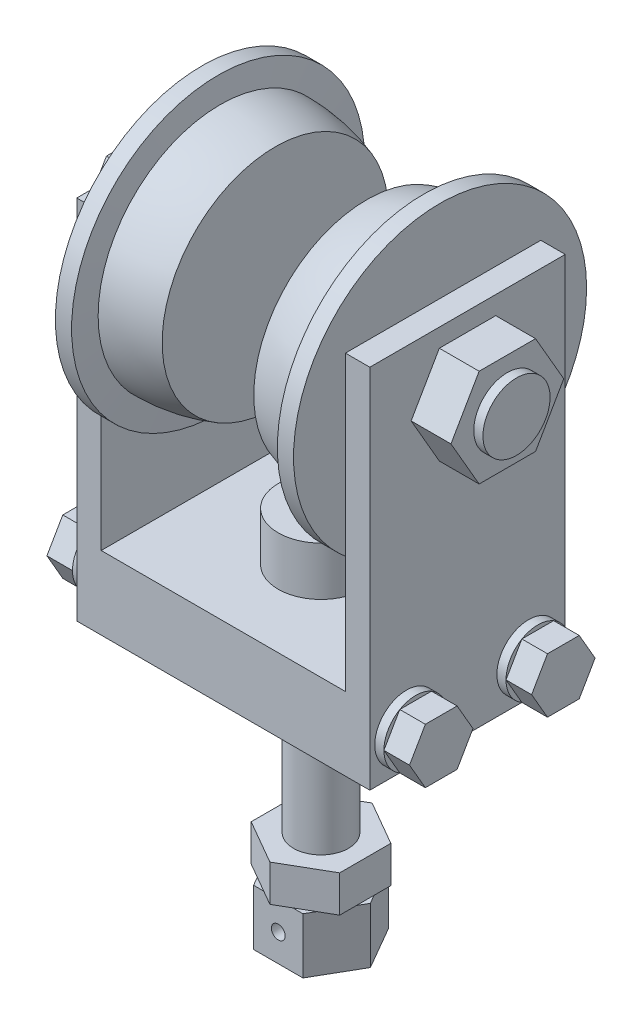
SolidWorks part; units mm, degrees
ref_plane "Front" through (0, 0, 0) normal (0, 0, 1) x (1, 0, 0)
ref_plane "Top" through (0, 0, 0) normal (0, 1, 0) x (1, 0, 0)
ref_plane "Right" through (0, 0, 0) normal (1, 0, 0) x (0, 0, -1)
ref_plane "Z PLANE" through (0, 0, 0) normal (0, 0, 1) x (1, 0, 0)
ref_plane "YOKE BOTTOM" through (0, 0, 0) normal (0, 1, 0) x (-1, 0, 0)
ref_plane "X PLANE" through (0, 0, 0) normal (1, 0, 0) x (0, 0, -1)
sketch "YOKE CROSS SECTION" plane through (0, 0, 0) normal (1, 0, 0) x (0, 0, -1)
  line L0 (0, 0) -> (0, 57.0916) construction
  line L1 (0, 84.8167) -> (0, -84.8167) construction
  line L2 (-50.8, 0) -> (50.8, 0)
  line L3 (69.1602, 0) -> (-69.1602, 0) construction
  line L4 (50.8, 0) -> (50.8, 38.1)
  line L5 (-50.8, 0) -> (-50.8, 38.1)
  line L6 (50.8, 38.1) -> (-50.8, 38.1)
  point P12 (0, 38.1)
  dimension "D1" = 38.1
  dimension "D2" = 101.6
ref_plane "1/2 YOKE LENGTH (A)" through (63.5, 0, 0) normal (1, 0, 0) x (0, 0, -1)
extrude "YOKE" add sketch "YOKE CROSS SECTION" along normal up to surface (63.5 mm away) up to plane "1/2 YOKE LENGTH (A)"
sketch "SIDEPLATE PROFILE" plane through (63.5, 0, 0) normal (1, 0, 0) x (0, 0, -1)
  line L0 (0, 0) -> (0, 74.7424) construction
  line L1 (0, 84.8167) -> (0, -84.8167) construction
  line L2 (-50.8, 0) -> (50.8, 0)
  line L3 (50.8, 0) -> (50.8, 190.5)
  line L4 (-50.8, 0) -> (-50.8, 190.5)
  line L5 (50.8, 190.5) -> (-50.8, 190.5)
  point P11 (0, 190.5)
  dimension "D1" = 190.5
ref_plane "WHEEL HEIGHT" through (0, 155.575, 0) normal (0, 1, 0) x (-1, 0, 0)
ref_plane "SCREW LOCATION X" through (0, 0, 31.75) normal (0, 0, 1) x (1, 0, 0)
ref_plane "SCREW LOCATION Y" through (0, 19.05, 0) normal (0, 1, 0) x (-1, 0, 0)
extrude "SIDEPLATE" add sketch "SIDEPLATE PROFILE" along normal blind 12.7
sketch "WHEEL PIN NUT PROFILE" plane through (76.2, 0, 0) normal (1, 0, 0) x (0, 0, -1)
  line L0 (0, 84.8167) -> (0, -84.8167) construction
  line L1 (29.3294, 155.575) -> (14.6647, 180.975)
  line L2 (14.6647, 180.975) -> (-14.6647, 180.975)
  line L3 (-14.6647, 180.975) -> (-29.3294, 155.575)
  line L4 (-29.3294, 155.575) -> (-14.6647, 130.175)
  line L5 (-14.6647, 130.175) -> (14.6647, 130.175)
  line L6 (14.6647, 130.175) -> (29.3294, 155.575)
  line L7 (69.1602, 155.575) -> (-69.1602, 155.575) construction
  circle A0 centre (0, 155.575) radius 25.4 construction
  dimension "D1" = 50.8
extrude "WHEEL PIN NUT" add sketch "WHEEL PIN NUT PROFILE" along normal blind 20.701
sketch "WHEEL PIN PROJECTION PROFILE" plane through (96.901, 0, 0) normal (1, 0, 0) x (0, 0, -1)
  line L0 (0, 84.8167) -> (0, -84.8167) construction
  line L1 (69.1602, 155.575) -> (-69.1602, 155.575) construction
  circle A0 centre (0, 155.575) radius 17.4625
  dimension "D1" = 34.925
extrude "WHEEL PIN PROJECTION" add sketch "WHEEL PIN PROJECTION PROFILE" along normal blind 4.7625
sketch "LOCKNUTS PROFILE" plane through (76.2, 0, 0) normal (1, 0, 0) x (0, 0, -1)
  line L0 (-31.75, 84.8167) -> (-31.75, -84.8167) construction
  line L1 (50, 19.05) -> (-50, 19.05) construction
  circle A0 centre (-31.75, 19.05) radius 16.4973
  dimension "D1" = 32.9946
extrude "LOCKNUTS" add sketch "LOCKNUTS PROFILE" along normal blind 4.7625
sketch "SCREWS PROFILE" plane through (80.9625, 0, 0) normal (1, 0, 0) x (0, 0, -1)
  line L0 (50, 19.05) -> (-50, 19.05) construction
  line L1 (-15.2522, 19.05) -> (-23.5011, 33.3375)
  line L2 (-23.5011, 33.3375) -> (-39.9989, 33.3375)
  line L3 (-39.9989, 33.3375) -> (-48.2478, 19.05)
  line L4 (-48.2478, 19.05) -> (-39.9989, 4.7625)
  line L5 (-39.9989, 4.7625) -> (-23.5011, 4.7625)
  line L6 (-23.5011, 4.7625) -> (-15.2522, 19.05)
  line L7 (-31.75, 84.8167) -> (-31.75, -84.8167) construction
  circle A0 centre (-31.75, 19.05) radius 14.2875 construction
  dimension "D1" = 28.575
extrude "SCREWS" add sketch "SCREWS PROFILE" along normal blind 13.3096
sketch "PROFILE" plane through (0, 38.1, 0) normal (0, 1, 0) x (-1, 0, 0)
  line L0 (84.8167, 0) -> (-84.8167, 0) construction
  line L1 (0, 83.2389) -> (0, -83.2389) construction
  circle A0 centre (0, 0) radius 22.225
  dimension "D1" = 44.45
extrude "KING BOLT HEAD" add sketch "PROFILE" along normal blind 25.4
mirror "Mirror1" about plane through (0, 0, 0) normal (0, 0, 1) of "SCREWS", "LOCKNUTS"
mirror "Mirror5" about plane through (0, 0, 0) normal (1, 0, 0) of bodies 112
ref_plane "TOP OF NUT" through (0, -82.55, 0) normal (0, 1, 0) x (-1, 0, 0)
sketch "DIA." plane through (0, 0, 0) normal (0, -1, 0) x (1, 0, 0)
  line L0 (84.8167, 0) -> (-84.8167, 0) construction
  line L1 (0, -83.2389) -> (0, 83.2389) construction
  circle A0 centre (0, 0) radius 14.2875
  dimension "D1" = 28.575
extrude "KING BOLT" add sketch "DIA." along normal up to surface (82.55 mm away) up to plane "TOP OF NUT"
sketch "KING BOLT JAN NUT PROFILE" plane through (0, -82.55, 0) normal (0, -1, 0) x (1, 0, 0)
  line L0 (84.8167, 0) -> (-84.8167, 0) construction
  line L1 (0, -26.5798) -> (23.0188, -13.2899)
  line L2 (23.0188, -13.2899) -> (23.0187, 13.2899)
  line L3 (23.0187, 13.2899) -> (0, 26.5798)
  line L4 (0, 26.5798) -> (-23.0188, 13.2899)
  line L5 (-23.0188, 13.2899) -> (-23.0188, -13.2899)
  line L6 (-23.0188, -13.2899) -> (0, -26.5798)
  line L7 (0, -83.2389) -> (0, 83.2389) construction
  circle A0 centre (0, 0) radius 23.0188 construction
  dimension "D1" = 46.0375
extrude "KING BOLT JAM NUT" add sketch "KING BOLT JAN NUT PROFILE" along normal blind 19.05
sketch "KING BOLT NUT PROFILE" plane through (0, -101.6, 0) normal (0, -1, 0) x (1, 0, 0)
  line L1 (25.6632, 0) -> (12.8316, 22.225)
  line L2 (12.8316, 22.225) -> (-12.8316, 22.225)
  line L3 (-12.8316, 22.225) -> (-25.6632, 0)
  line L4 (-25.6632, 0) -> (-12.8316, -22.225)
  line L5 (-12.8316, -22.225) -> (12.8316, -22.225)
  line L6 (12.8316, -22.225) -> (25.6632, 0)
  line L10 (0, -83.2389) -> (0, 83.2389) construction
  line L11 (84.8167, 0) -> (-84.8167, 0) construction
  circle A0 centre (0, 0) radius 22.225 construction
  dimension "D1" = 44.45
extrude "KING BOLT NUT" add sketch "KING BOLT NUT PROFILE" along normal blind 28.9306
sketch "Sketch5" plane through (0, -130.5306, 0) normal (0, -1, 0) x (1, 0, 0)
  circle A0 centre (0, 0) radius 14.2875 construction
  circle A1 centre (0, 0) radius 14.2875
extrude "EXTENDED KING BOLT" add sketch "Sketch5" along normal blind 6.35
chamfer "Chamfer1" distance 2.3812 angle 45 1 edges at (0, -136.8806, -14.2875)
ref_plane "MOUNTING REF PLANE" through (0, -34.925, 0) normal (0, 1, 0) x (-1, 0, 0)
sketch "Sketch6" plane through (0, 0, 0) normal (0, 0, 1) x (1, 0, 0)
  line L0 (61.9125, 180.975) -> (61.9125, 231.775)
  line L1 (63.5, 180.975) -> (63.5, 155.575)
  line L2 (23.8125, 155.575) -> (23.8125, 214.3574)
  line L3 (23.8125, 155.575) -> (63.5, 155.575)
  line L4 (61.9125, 180.975) -> (63.5, 180.975)
  line L5 (52.3875, 219.075) -> (53.4986, 231.775)
  line L6 (61.9125, 231.775) -> (53.4986, 231.775)
  line L8 (69.1602, 155.575) -> (-69.1602, 155.575) construction
  line L9 (63.5, -75.0522) -> (63.5, 75.0522) construction
  arc A0 (52.3875, 219.075) -> (23.8125, 214.3574) centre (52.3875, 130.175) ccw
  dimension "D4" = 88.9
  dimension "D1" = 39.6875
  dimension "D2" = 25.4
  dimension "D3" = 58.7824
  dimension "D5" = 76.2
  dimension "D6" = 1.5875
  dimension "D7" = 10.0014
  dimension "D8" = 11.1125
  dimension "D9" = 63.5
  dimension "D10" = 39.6875
revolve "WHEEL" add sketch "Sketch6" angle 360 about axis through (101.6635, 155.575, 0) along (-1, 0, 0)
mirror "Mirror6" about plane through (0, 0, 0) normal (1, 0, 0) of "WHEEL"
sketch "Sketch7" plane through (0, 0, 22.225) normal (0, 0, 1) x (1, 0, 0)
  line L0 (0, -83.2389) -> (0, 83.2389) construction
  line L1 (-12.8316, -130.5306) -> (-25.6632, -130.5306) construction
  circle A0 centre (0, -116.2431) radius 3.5719
  dimension "D1" = 7.1437
  dimension "D2" = 14.2875
extrude "COTTER PIN HOLE" cut sketch "Sketch7" against normal up to next
sketch "Sketch8" plane through (0, 0, 0) normal (0, -1, 0) x (1, 0, 0)
  circle A0 centre (0, 0) radius 25.4
  circle A1 centre (0, 0) radius 30.1625
  dimension "D1" = 50.8
  dimension "D2" = 60.325
extrude "SPACER" add sketch "Sketch8" along normal blind 12.7
ref_plane "TREAD OF TRACK" through (0, 92.075, 0) normal (0, 1, 0) x (-1, 0, 0)
